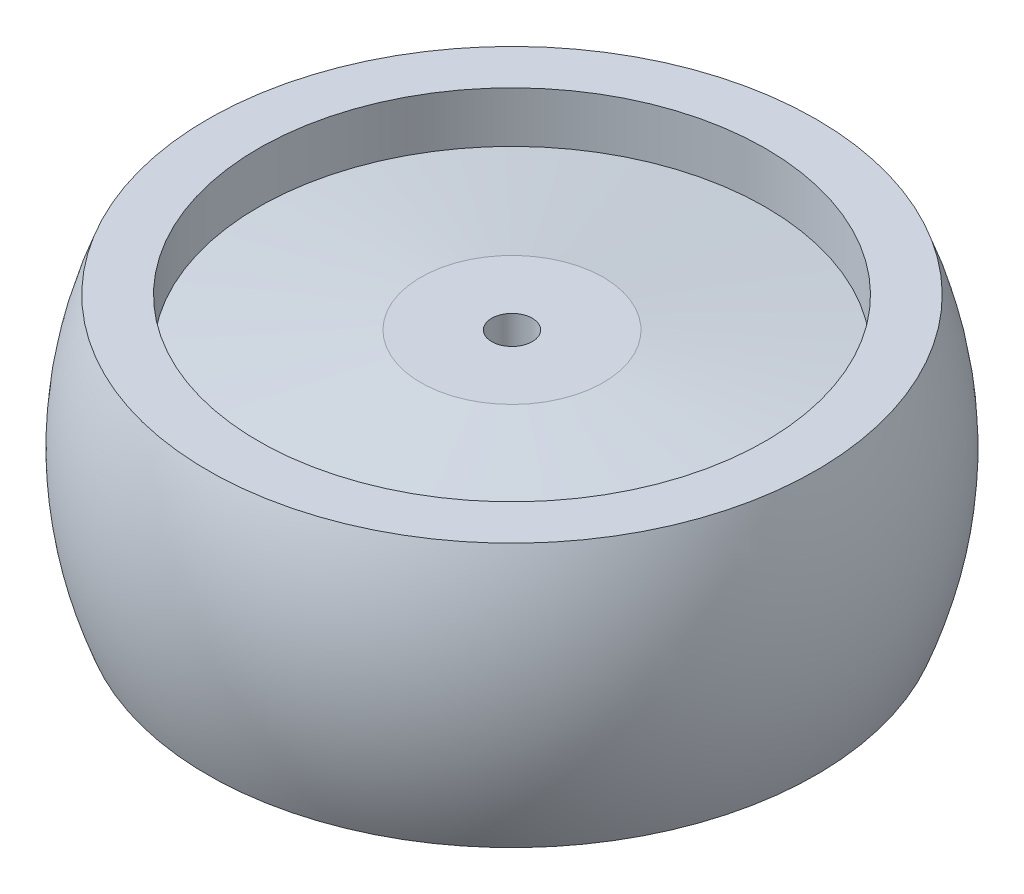
SolidWorks part; units mm, degrees
ref_plane "Front Plane" through (0, 0, 0) normal (0, 0, 1) x (1, 0, 0)
ref_plane "Top Plane" through (0, 0, 0) normal (0, 1, 0) x (1, 0, 0)
ref_plane "Right Plane" through (0, 0, 0) normal (1, 0, 0) x (0, 0, -1)
sketch "Sketch1" plane through (0, 0, 0) normal (0, 0, 1) x (1, 0, 0)
  line L0 (-25, 8) -> (-9, 10)
  line L1 (0, -13) -> (-30, -13)
  line L2 (0, -13) -> (0, 13)
  line L3 (0, 13) -> (-30, 13)
  line L4 (-30, -13) -> (-30, 13)
  line L5 (-30, 13) -> (-25, 13)
  line L6 (-30, 13) -> (-30, -13)
  line L7 (-30, -13) -> (-25, -13)
  line L8 (-25, 13) -> (-25, -13)
  line L9 (0, 10) -> (-9, 10)
  line L10 (0, 10) -> (0, 5)
  line L11 (0, 5) -> (-9, 5)
  line L12 (-9, 10) -> (-9, 5)
  line L13 (-25, 3.9689) -> (-9, 5.9689)
  spline S0 degree 2 poles (-30, 13) (-35, 0) (-30, -13) knots 0 0 0 1 1 1
  point P5 (-25, 8)
  point P6 (0, 0)
  point P17 (-9, 5.9563)
  dimension "D1" = 2.5
  dimension "D2" = 32.5
  dimension "D3" = 26
  dimension "D4" = 5
  dimension "D5" = 3
  dimension "D6" = 5
  dimension "D7" = 9
  dimension "D8" = 18
  dimension "D9" = 4
revolve "Revolve1" add sketch "Sketch1" angle 360 about L2
sketch "Sketch2" plane through (0, 5, 0) normal (0, -1, 0) x (1, 0, 0)
  circle A0 centre (0, 0) radius 8
  dimension "D1" = 16
extrude "Boss-Extrude1" add sketch "Sketch2" along normal blind 6
sketch "Sketch3" plane through (0, -1, 0) normal (0, -1, 0) x (1, 0, 0)
  line L1 (6.9282, 0) -> (3.4641, 6)
  line L2 (3.4641, 6) -> (-3.4641, 6)
  line L3 (-3.4641, 6) -> (-6.9282, 0)
  line L4 (-6.9282, 0) -> (-3.4641, -6)
  line L5 (-3.4641, -6) -> (3.4641, -6)
  line L6 (3.4641, -6) -> (6.9282, 0)
  circle A0 centre (0, 0) radius 6 construction
  point P1 (0, 0)
  dimension "D1" = 12
extrude "Cut-Extrude1" cut sketch "Sketch3" against normal blind 5
sketch "Sketch4" plane through (0, 4, 0) normal (0, -1, 0) x (1, 0, 0)
  circle A0 centre (0, 0) radius 2
  dimension "D1" = 4
extrude "Cut-Extrude2" cut sketch "Sketch4" against normal through all
